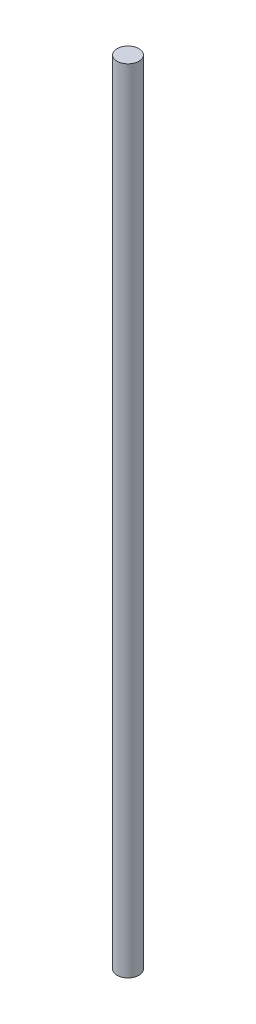
SolidWorks part; units mm, degrees
material "1023 Carbon Steel Sheet (SS)"
ref_plane "Front Plane" through (0, 0, 0) normal (0, 0, 1) x (1, 0, 0)
ref_plane "Top Plane" through (0, 0, 0) normal (0, 1, 0) x (1, 0, 0)
ref_plane "Right Plane" through (0, 0, 0) normal (1, 0, 0) x (0, 0, -1)
sketch "Sketch1" plane through (0, 0, 0) normal (0, 1, 0) x (1, 0, 0)
  circle A0 centre (0, 0) radius 3.175
  dimension "D1" = 6.35
extrude "Boss-Extrude1" add sketch "Sketch1" along normal blind 230
